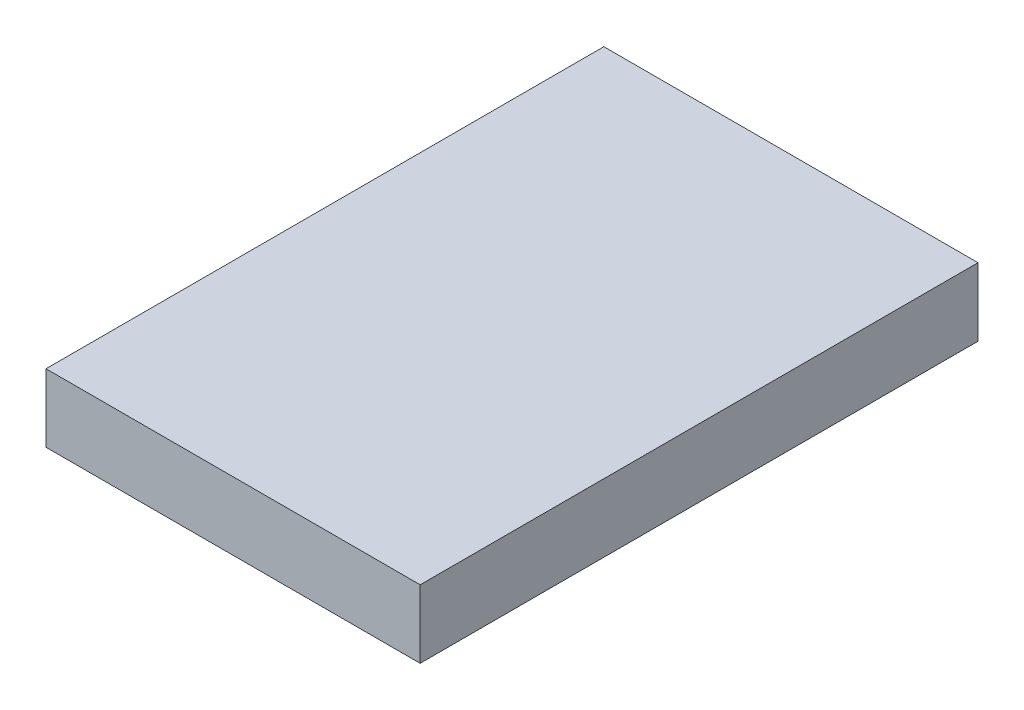
SolidWorks part; units mm, degrees
ref_plane "Front Plane" through (0, 0, 0) normal (0, 0, 1) x (1, 0, 0)
ref_plane "Top Plane" through (0, 0, 0) normal (0, 1, 0) x (1, 0, 0)
ref_plane "Right Plane" through (0, 0, 0) normal (1, 0, 0) x (0, 0, -1)
sketch "Sketch1" plane through (0, 0, 0) normal (0, 1, 0) x (1, 0, 0)
  line L1 (-27.5, 41) -> (27.5, 41)
  line L2 (-27.5, 41) -> (-27.5, -41)
  line L3 (-27.5, -41) -> (27.5, -41)
  line L4 (27.5, 41) -> (27.5, -41)
  line L5 (-27.5, 41) -> (27.5, -41) construction
  line L6 (-27.5, -41) -> (27.5, 41) construction
  point P0 (0, 0)
  dimension "D1" = 55
  dimension "D2" = 82
extrude "Boss-Extrude1" add sketch "Sketch1" along normal blind 10
